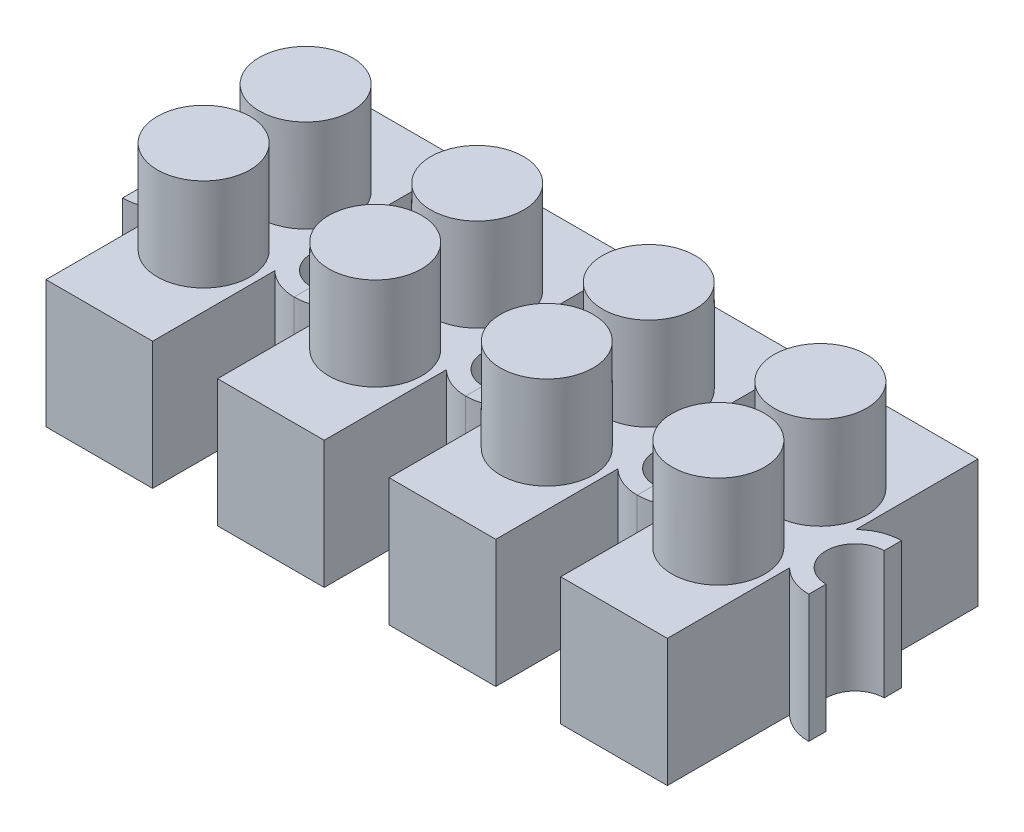
SolidWorks part; units mm, degrees
ref_plane "Front Plane" through (0, 0, 0) normal (0, 0, 1) x (1, 0, 0)
ref_plane "Top Plane" through (0, 0, 0) normal (0, 1, 0) x (1, 0, 0)
ref_plane "Right Plane" through (0, 0, 0) normal (1, 0, 0) x (0, 0, -1)
sketch "Sketch2" plane through (0, 0, 0) normal (0, 1, 0) x (1, 0, 0)
  line L0 (2.921, 8.509) -> (-2.921, 8.509)
  line L1 (-2.921, 8.509) -> (-2.921, 1.8139)
  line L2 (0, -9.3599) -> (0, 9.3599) construction
  line L3 (2.921, 8.509) -> (2.921, 1.8139)
  line L4 (-5.1689, 0) -> (5.1689, 0) construction
  line L5 (-2.921, -8.509) -> (-2.921, -1.8139)
  line L6 (2.921, -8.509) -> (2.921, -1.8139)
  line L7 (2.921, -8.509) -> (-2.921, -8.509)
  line L8 (-4.699, 2.54) -> (-4.699, -2.54) construction
  line L9 (4.699, 2.54) -> (4.699, -2.54) construction
  line L10 (-4.699, 1.5875) -> (-4.699, 2.54)
  line L11 (-4.699, -2.54) -> (-4.699, -1.5875)
  line L12 (4.699, -2.54) -> (4.699, -1.5875)
  line L13 (4.699, 1.5875) -> (4.699, 2.54)
  arc A0 (-4.699, -2.54) -> (-2.921, -1.8139) centre (-4.699, 0) ccw
  arc A1 (-4.699, 2.54) -> (-2.921, 1.8139) centre (-4.699, 0) cw
  arc A2 (4.699, -2.54) -> (2.921, -1.8139) centre (4.699, 0) cw
  arc A3 (4.699, 2.54) -> (2.921, 1.8139) centre (4.699, 0) ccw
  arc A4 (-4.699, 1.5875) -> (-4.699, -1.5875) centre (-4.699, 0) cw
  arc A5 (4.699, 1.5875) -> (4.699, -1.5875) centre (4.699, 0) ccw
  point P7 (0, 8.509)
  point P17 (-4.699, 0)
  point P18 (4.699, 0)
  point P25 (-4.699, 2.54)
  point P26 (4.699, -2.54)
  point P27 (2.921, -8.509)
  dimension "D1" = 1.5875
  dimension "D2" = 5.842
  dimension "D3" = 1.778
  dimension "D4" = 5.08
  dimension "D5" = 17.018
extrude "Boss-Extrude1" add sketch "Sketch2" along normal blind 6.985 contours L3 A3 L13 A5 L12 A2 L6 L7 L5 A0 L11 A4 L10 A1 L1 L0
sketch "Sketch3" plane through (0, 0, 0) normal (0, -1, 0) x (1, 0, 0)
  line L1 (-2.286, 7.747) -> (2.286, 7.747)
  line L2 (-2.286, 7.747) -> (-2.286, -7.747)
  line L3 (-2.286, -7.747) -> (2.286, -7.747)
  line L4 (2.286, 7.747) -> (2.286, -7.747)
  line L5 (0, -7.747) -> (0, 7.747) construction
  point P4 (0, 7.747)
  point P6 (2.286, 0)
  point P7 (-2.286, 0)
  point P8 (0, -7.747)
  point P9 (0, 0)
  point P10 (0, 0)
  dimension "D1" = 4.572
  dimension "D2" = 15.494
extrude "Cut-Extrude1" cut sketch "Sketch3" against normal blind 1.27
sketch "Sketch6" plane through (0, 6.985, 0) normal (0, 1, 0) x (1, 0, 0)
  line L0 (0, -3.8418) -> (0, 3.8418) construction
  line L1 (0, 2.794) -> (0, -2.794) construction
  line L2 (-3.8418, 0) -> (3.8418, 0) construction
  line L3 (0, -5.334) -> (0, 5.334) construction
  circle A0 centre (0, 2.794) radius 2.54
  circle A1 centre (0, -2.794) radius 2.54
  point P6 (0, 0)
  dimension "D1" = 5.08
  dimension "D2" = 10.668
extrude "Boss-Extrude3" add sketch "Sketch6" along normal blind 5.08
pattern_linear "LPattern1" count 4 spacing 9.398 along (-1, 0, 0) of bodies 104
equation "\"Terminals\"= 4"
